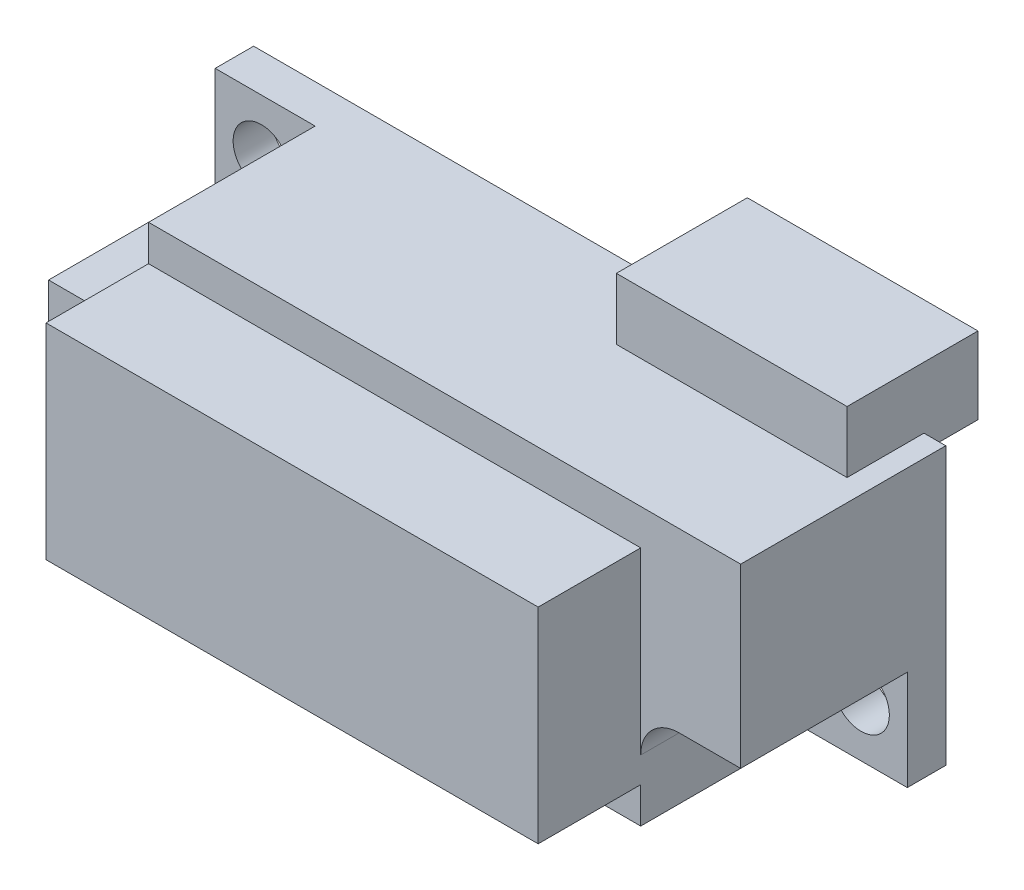
SolidWorks part; units mm, degrees
ref_plane "Front Plane" through (0, 0, 0) normal (0, 0, 1) x (1, 0, 0)
ref_plane "Top Plane" through (0, 0, 0) normal (0, 1, 0) x (1, 0, 0)
ref_plane "Right Plane" through (0, 0, 0) normal (1, 0, 0) x (0, 0, -1)
sketch "스케치1" plane through (0, 0, 0) normal (0, 0, 1) x (1, 0, 0)
  line L1 (-26.1453, 14.8512) -> (0.8547, 14.8512)
  line L2 (-26.1453, 14.8512) -> (-26.1453, 4.0512)
  line L3 (-26.1453, 4.0512) -> (0.8547, 4.0512)
  line L4 (0.8547, 14.8512) -> (0.8547, 4.0512)
  dimension "D1" = 27
  dimension "D2" = 10.8
extrude "보스-돌출1" add sketch "스케치1" along normal blind 12
sketch "스케치2" plane through (0, 0, 12) normal (0, 0, 1) x (1, 0, 0)
  line L0 (-3.0453, 6.6047) -> (-3.0453, -49993.3953) construction
  line L1 (-1.5019, 7.9512) -> (49998.4981, 7.9512) construction
  line L2 (-22.2453, 12.6216) -> (-22.2453, -49987.3784) construction
  line L3 (-26.1453, 10.9512) -> (49973.8547, 10.9512) construction
  line L5 (-26.1453, 14.8512) -> (-26.1453, 4.0512) construction
  line L6 (0.8547, 14.8512) -> (-26.1453, 14.8512) construction
  line L7 (0.8547, 4.0512) -> (0.8547, 14.8512) construction
  line L8 (-26.1453, 4.0512) -> (0.8547, 4.0512) construction
  line L10 (-26.1453, 14.8512) -> (-22.2453, 14.8512)
  line L11 (-26.1453, 14.8512) -> (-26.1453, 10.9512)
  line L12 (-26.1453, 10.9512) -> (-22.2453, 10.9512)
  line L13 (-22.2453, 14.8512) -> (-22.2453, 10.9512)
  line L14 (-3.0453, 7.9512) -> (0.8547, 7.9512)
  line L15 (-3.0453, 7.9512) -> (-3.0453, 4.0512)
  line L16 (-3.0453, 4.0512) -> (0.8547, 4.0512)
  line L17 (0.8547, 7.9512) -> (0.8547, 4.0512)
  dimension "D1" = 3.9
  dimension "D2" = 3.9
  dimension "D3" = 3.9
  dimension "D4" = 3.9
extrude "컷-돌출2" cut sketch "스케치2" against normal blind 10.5
fillet "필렛3" radius 1.5 1 edges at (-22.2453, 10.9512, 6.75)
fillet "필렛4" radius 1.5 1 edges at (-3.0453, 7.9512, 6.75)
sketch "스케치3" plane through (0, 0, 1.5) normal (0, 0, 1) x (1, 0, 0)
  line L0 (-24.3453, 12.9454) -> (-24.3453, -49987.0546) construction
  line L1 (-24.6521, 12.7512) -> (49975.3479, 12.7512) construction
  line L2 (-0.9453, 5.9301) -> (-0.9453, -49994.0699) construction
  line L3 (-1.9605, 6.1512) -> (49998.0395, 6.1512) construction
  line L5 (-26.1453, 14.8512) -> (-26.1453, 10.9512) construction
  line L6 (-22.2453, 14.8512) -> (-26.1453, 14.8512) construction
  line L7 (-3.0453, 4.0512) -> (0.8547, 4.0512) construction
  line L8 (0.8547, 4.0512) -> (0.8547, 7.9512) construction
  circle A0 centre (-24.3453, 12.7512) radius 1.1
  circle A1 centre (-0.9453, 6.1512) radius 1.1
  dimension "D1" = 1.8
  dimension "D2" = 2.1
  dimension "D3" = 2.1
  dimension "D4" = 1.8
extrude "컷-돌출3" cut sketch "스케치3" against normal blind 2.1
sketch "스케치4" plane through (0, 0, 12) normal (0, 0, 1) x (1, 0, 0)
  line L0 (0.8547, 7.9512) -> (0.8547, 14.8512) construction
  line L1 (-22.2453, 13.4512) -> (-3.0453, 13.4512)
  line L2 (-22.2453, 13.4512) -> (-22.2453, 5.4512)
  line L3 (-22.2453, 5.4512) -> (-3.0453, 5.4512)
  line L4 (-3.0453, 13.4512) -> (-3.0453, 5.4512)
  line L5 (-26.1453, 4.0512) -> (-3.0453, 4.0512) construction
  line L7 (-26.1453, 14.8512) -> (0.8547, 14.8512)
  line L8 (-26.1453, 14.8512) -> (-26.1453, 4.0512)
  line L9 (-26.1453, 4.0512) -> (0.8547, 4.0512)
  line L10 (0.8547, 14.8512) -> (0.8547, 4.0512)
  dimension "D1" = 8
  dimension "D2" = 19.2
  dimension "D3" = 3.9
  dimension "D4" = 1.4
extrude "컷-돌출4" cut sketch "스케치4" against normal blind 4
sketch "스케치5" plane through (0, 0, 0) normal (0, 0, -1) x (-1, 0, 0)
  line L0 (26.1453, 4.0512) -> (-0.8547, 4.0512) construction
  line L1 (-0.0047, 17.2512) -> (8.9953, 17.2512)
  line L2 (-0.0047, 17.2512) -> (-0.0047, 14.2512)
  line L3 (-0.0047, 14.2512) -> (8.9953, 14.2512)
  line L4 (8.9953, 17.2512) -> (8.9953, 14.2512)
  line L5 (-0.8547, 4.0512) -> (-0.8547, 14.8512) construction
  dimension "D1" = 13.2
  dimension "D2" = 3
  dimension "D3" = 9
  dimension "D4" = 9.85
extrude "보스-돌출2" add sketch "스케치5" along normal blind 2.108 and the other way blind 3
